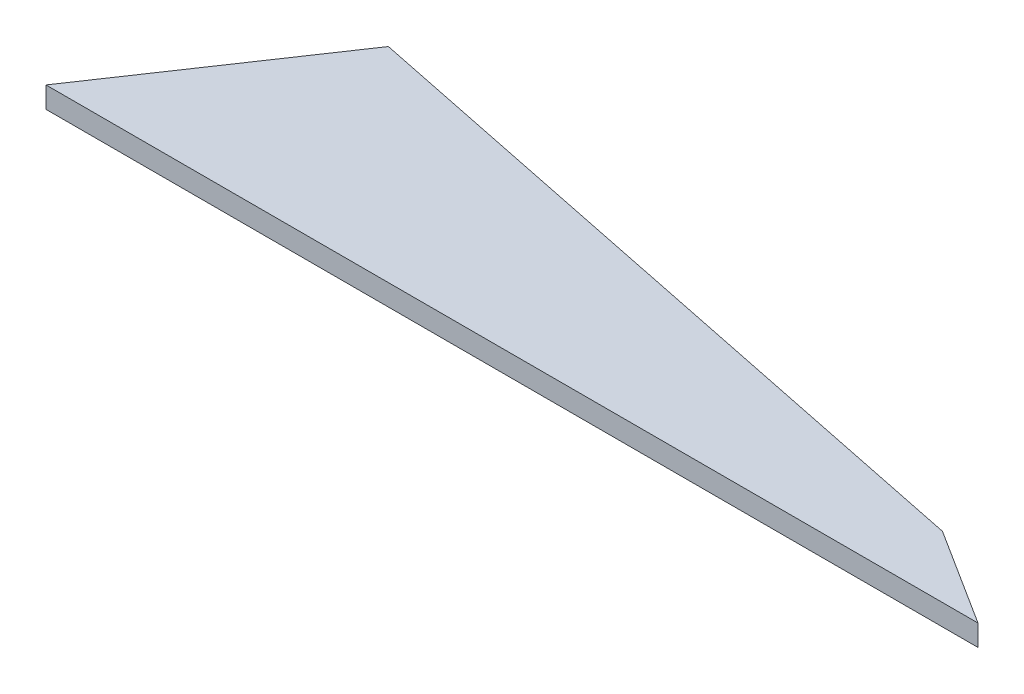
SolidWorks part; units mm, degrees
ref_plane "Plan de face" through (0, 0, 0) normal (0, 0, 1) x (1, 0, 0)
ref_plane "Plan de dessus" through (0, 0, 0) normal (0, 1, 0) x (1, 0, 0)
ref_plane "Plan de droite" through (0, 0, 0) normal (1, 0, 0) x (0, 0, -1)
sketch "Esquisse1" plane through (0, 0, 0) normal (0, 1, 0) x (1, 0, 0)
  line L0 (88.0491, 0) -> (78.861, 5.8298)
  line L1 (78.861, 5.8298) -> (13.0307, 19.3145)
  line L2 (13.0307, 19.3145) -> (0, 0)
  line L3 (0, 0) -> (88.0491, 0)
  point P4 (0, 0)
extrude "Boss.-Extru.1" add sketch "Esquisse1" along normal blind 2
